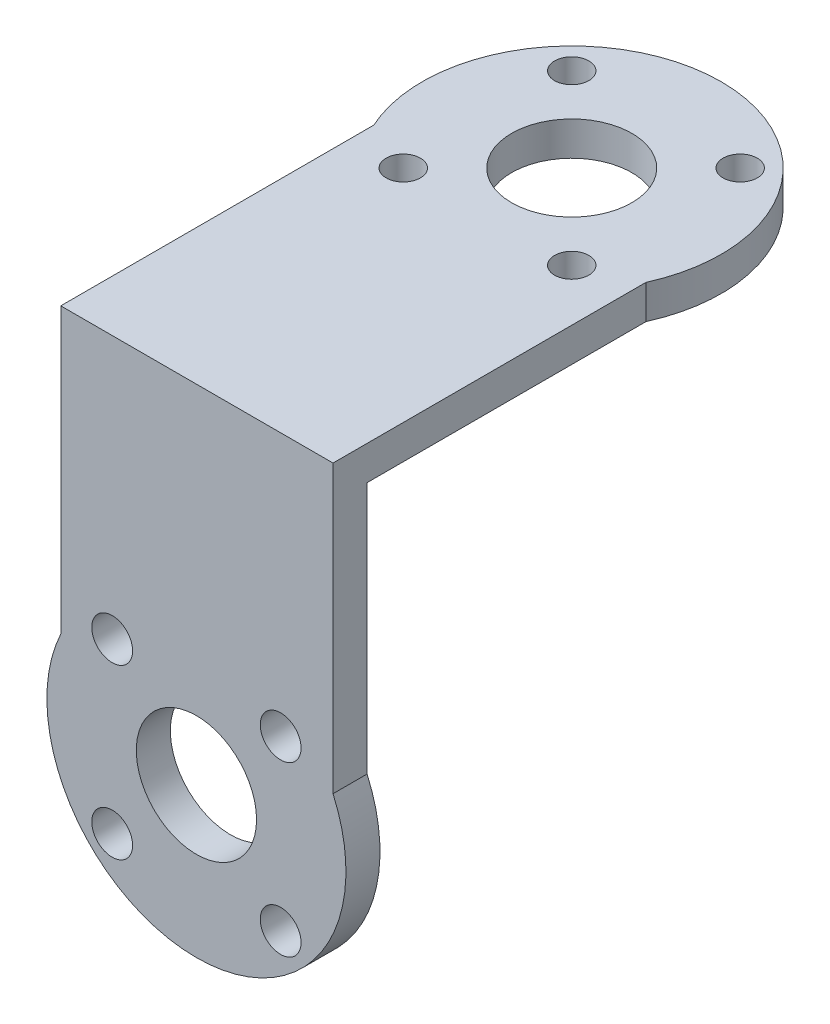
SolidWorks part; units mm, degrees
ref_plane "Alzado" through (0, 0, 0) normal (0, 0, 1) x (1, 0, 0)
ref_plane "Planta" through (0, 0, 0) normal (0, 1, 0) x (1, 0, 0)
ref_plane "Vista lateral" through (0, 0, 0) normal (1, 0, 0) x (0, 0, -1)
sketch "Croquis1" plane through (0, 0, 0) normal (0, 1, 0) x (1, 0, 0)
  line L1 (-14.5307, 6.5843) -> (11.8293, 6.5843) construction
  line L2 (10.6493, -23.4557) -> (10.6493, 1.1334)
  line L3 (-13.3507, -23.4557) -> (10.6493, -23.4557)
  line L4 (-1.3507, -23.4557) -> (-1.3507, 6.5843) construction
  line L5 (-13.3507, -23.4557) -> (-13.3507, 1.1334)
  line L7 (-13.3507, -23.4557) -> (-22.6274, -23.4557) construction
  line L8 (-1.3507, 6.5843) -> (10.5865, 18.5215) construction
  arc A0 (10.6493, 1.1334) -> (-13.3507, 1.1334) centre (-1.3507, 6.5843) ccw
  circle A1 centre (-1.3507, 6.5843) radius 5.3
  circle A2 centre (-1.3507, 6.5843) radius 13.18 construction
  circle A3 centre (-1.3507, 6.5843) radius 10.5 construction
  circle A4 centre (6.0739, 14.0089) radius 1.5114
  circle A5 centre (6.0739, -0.8403) radius 1.5114
  circle A6 centre (-8.7753, -0.8403) radius 1.5114
  circle A7 centre (-8.7753, 14.0089) radius 1.5114
  point P0 (0, 0)
  point P25 (-1.3507, 6.5843)
  dimension "D1" = 24
  dimension "D3" = 10.6
  dimension "D4" = 45
  dimension "D6" = 21
  dimension "D7" = 26.36
  dimension "D2" = 30.04
  dimension "D5" = 4
extrude "Saliente-Extruir1" add sketch "Croquis1" along normal blind 3
sketch "Croquis3" plane through (0, 0, 23.4557) normal (0, 0, 1) x (1, 0, 0)
  line L0 (-1.3929, -27.6) -> (-1.3507, 3) construction
  line L1 (10.6493, 3) -> (-13.3507, 3)
  line L2 (10.6493, 3) -> (10.6493, -22.2429)
  line L3 (11.7871, -27.6) -> (-14.5729, -27.6) construction
  line L4 (-13.3507, 3) -> (-13.3507, -22.0572)
  line L5 (-1.3929, -27.6) -> (-11.8282, -38.0353) construction
  line L6 (-13.3507, 3) -> (10.6493, 3) construction
  line L7 (-1.3929, -40.78) -> (25.7521, -40.78) construction
  arc A0 (-13.3507, -22.0572) -> (10.6493, -22.2429) centre (-1.3929, -27.6) ccw
  circle A1 centre (-1.3929, -27.6) radius 13.18 construction
  circle A2 centre (-1.3929, -27.6) radius 10.5 construction
  circle A3 centre (-8.8175, -35.0246) radius 1.8
  circle A4 centre (-8.8175, -20.1754) radius 1.8
  circle A5 centre (6.0318, -20.1754) radius 1.8
  circle A6 centre (6.0318, -35.0246) radius 1.8
  circle A7 centre (-1.3929, -27.6) radius 5.3
  point P21 (-1.3929, -27.6)
  dimension "D2" = 3.6
  dimension "D4" = 26.36
  dimension "D6" = 10.6
  dimension "D7" = 21
  dimension "D1" = 45
  dimension "D5" = 30.6
  dimension "D3" = 4
extrude "Saliente-Extruir2" add sketch "Croquis3" along normal blind 3
